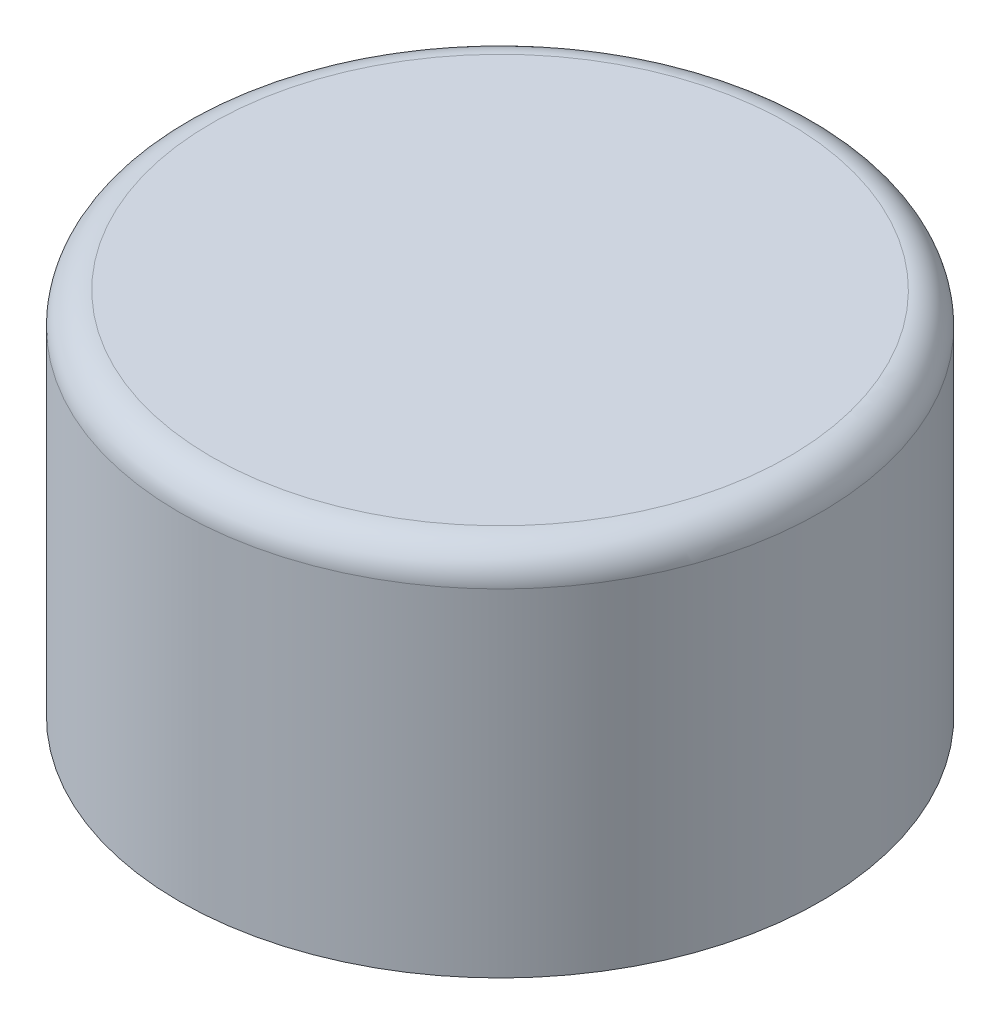
SolidWorks part; units mm, degrees
material "PVC Rigid"
ref_plane "Front Plane" through (0, 0, 0) normal (0, 0, 1) x (1, 0, 0)
ref_plane "Top Plane" through (0, 0, 0) normal (0, 1, 0) x (1, 0, 0)
ref_plane "Right Plane" through (0, 0, 0) normal (1, 0, 0) x (0, 0, -1)
sketch "Sketch2" plane through (0, 0, 0) normal (0, 1, 0) x (1, 0, 0)
  circle A0 centre (0, 0) radius 44.45
  circle A1 centre (0, 0) radius 50.8
  dimension "D1" = 88.9
  dimension "D2" = 6.35
extrude "Boss-Extrude2" add sketch "Sketch2" along normal blind 50.8 separate body
sketch "Sketch6" plane through (0, 50.8, 0) normal (0, 1, 0) x (1, 0, 0)
  circle A0 centre (0, 0) radius 50.8
extrude "Boss-Extrude3" add sketch "Sketch6" along normal blind 7.62
fillet "Fillet1" radius 5.08 1 edges at (0, 58.42, 50.8)
